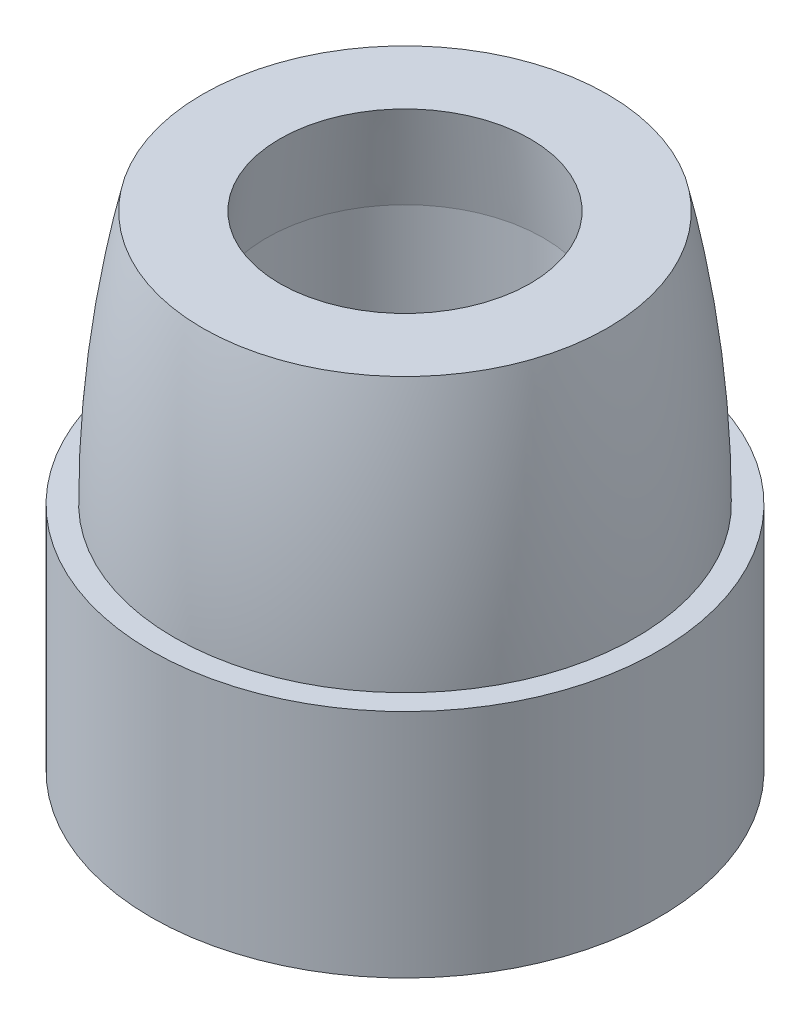
SolidWorks part; units mm, degrees
ref_plane "Спереди" through (0, 0, 0) normal (0, 0, 1) x (1, 0, 0)
ref_plane "Сверху" through (0, 0, 0) normal (0, 1, 0) x (1, 0, 0)
ref_plane "Справа" through (0, 0, 0) normal (1, 0, 0) x (0, 0, -1)
sketch "Эскиз1" plane through (0, 0, 0) normal (0, 0, 1) x (1, 0, 0)
  line L0 (0, 0) -> (0, 12) construction
  line L1 (3, 0) -> (5.5, 0)
  line L2 (5.5, 0) -> (5.5, 5)
  line L3 (4, 12) -> (2.5, 12)
  line L4 (5.5, 5) -> (5, 5)
  line L5 (0, 0) -> (0, 12) construction
  line L6 (2.5, 12) -> (3, 8.5)
  line L7 (3, 8.5) -> (3, 0)
  line L8 (3, 0) -> (0, 0) construction
  line L9 (2.5, 12) -> (0, 12) construction
  arc A0 (5, 5) -> (4, 12) centre (-20, 5) ccw
  dimension "D1" = 11
  dimension "D4" = 8
  dimension "D2" = 5
  dimension "D3" = 12
  dimension "D5" = 0.5
  dimension "D6" = 3.5
  dimension "D7" = 3
  dimension "D8" = 2.5
revolve "Повернуть1" add sketch "Эскиз1" angle 360 about L0
sketch "Эскиз2" plane through (0, 0, 0) normal (0, -1, 0) x (1, 0, 0)
  circle A0 centre (0, 0) radius 4
  dimension "D1" = 8
extrude "Вырез-Вытянуть1" cut sketch "Эскиз2" against normal blind 4
sketch "Эскиз3" plane through (0, 12, 0) normal (0, 1, 0) x (1, 0, 0)
  circle A0 centre (0, 0) radius 2.5 construction
  circle A1 centre (0, 0) radius 2.5
  circle A2 centre (0, 0) radius 5.5 construction
  circle A3 centre (0, 0) radius 5.5
extrude "Вырез-Вытянуть2" cut sketch "Эскиз3" against normal blind 1.5
